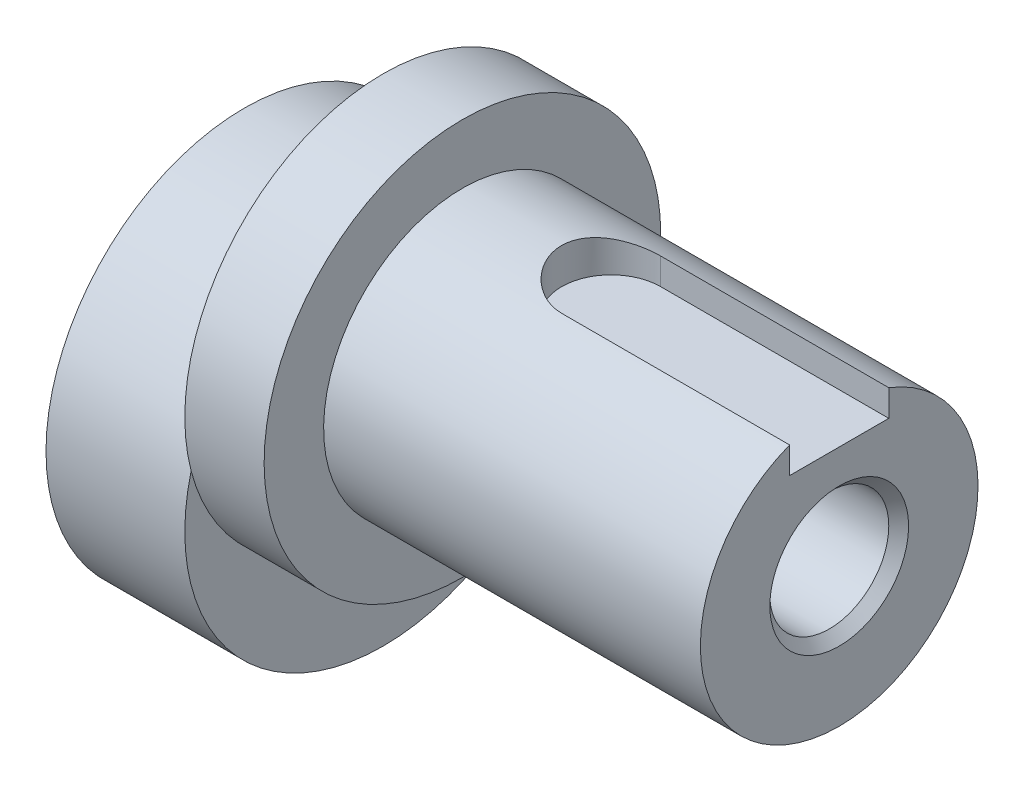
SolidWorks part; units mm, degrees
ref_plane "Front Plane" through (0, 0, 0) normal (0, 0, 1) x (1, 0, 0)
ref_plane "Top Plane" through (0, 0, 0) normal (0, 1, 0) x (1, 0, 0)
ref_plane "Right Plane" through (0, 0, 0) normal (1, 0, 0) x (0, 0, -1)
sketch "Sketch1" plane through (0, 0, 0) normal (1, 0, 0) x (0, 0, -1)
  circle A0 centre (0, 0) radius 10
  dimension "D1" = 20
extrude "Boss-Extrude1" add sketch "Sketch1" along normal blind 7
sketch "Sketch2" plane through (7, 0, 0) normal (1, 0, 0) x (0, 0, -1)
  circle A0 centre (0, 5) radius 10
  dimension "D1" = 20
  dimension "D2" = 5
extrude "Boss-Extrude2" add sketch "Sketch2" along normal blind 4
sketch "Sketch3" plane through (11, 0, 0) normal (1, 0, 0) x (0, 0, -1)
  circle A0 centre (0, 5) radius 7
  dimension "D1" = 14
extrude "Boss-Extrude3" add sketch "Sketch3" along normal blind 19
sketch "Sketch4" plane through (30, 0, 0) normal (1, 0, 0) x (0, 0, -1)
  circle A0 centre (0, 5) radius 3
  dimension "D1" = 6
extrude "Cut-Extrude1" cut sketch "Sketch4" against normal through all
chamfer "Chamfer1" distance 0.5 angle 45 2 edges at (30, 5, -3) (0, 5, -3)
sketch "Sketch5" plane through (0, 0, 0) normal (0, 1, 0) x (1, 0, 0)
  line L0 (30, 0) -> (14.3442, 0) construction
  line L1 (30, -7) -> (30, 7) construction
  line L3 (31, 2.5) -> (18.5, 2.5)
  line L4 (31, 2.5) -> (31, -2.5)
  line L5 (31, -2.5) -> (18.5, -2.5)
  arc A0 (18.5, 2.5) -> (18.5, -2.5) centre (18.5, 0) ccw
  point P10 (16, 0)
  dimension "D1" = 2.5
  dimension "D2" = 14
  dimension "D3" = 1
extrude "Cut-Extrude2" cut sketch "Sketch5" along normal through all from offset 10.2
